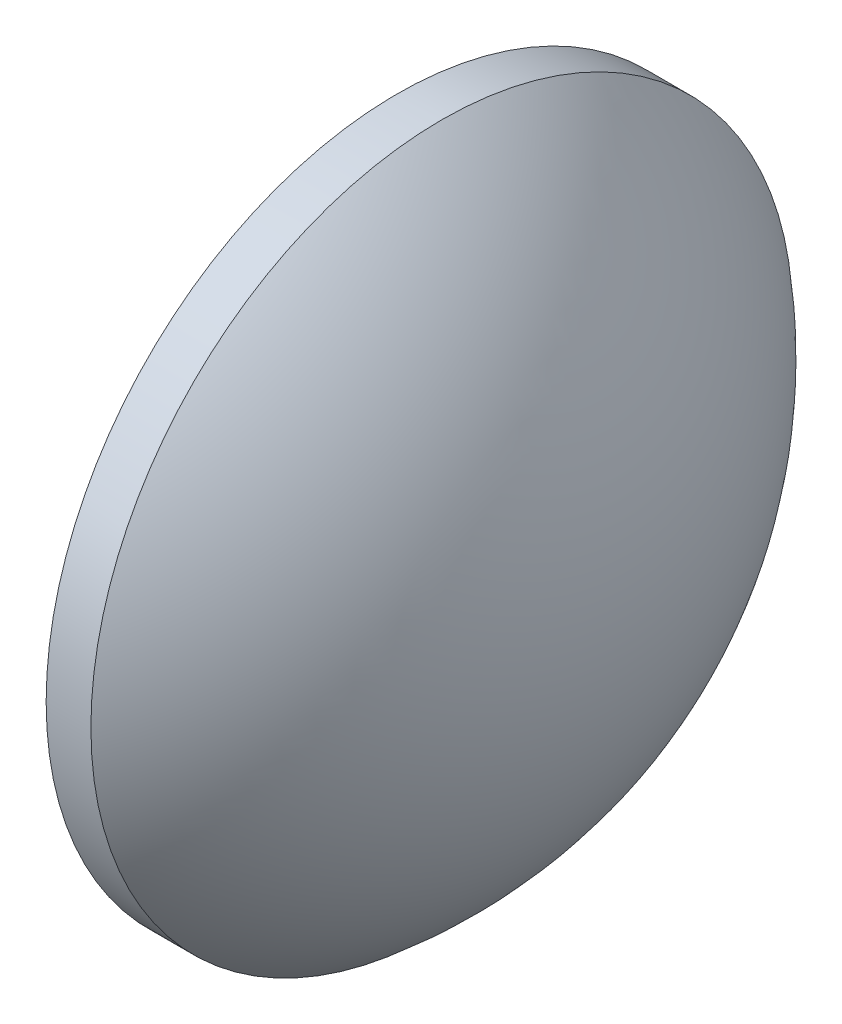
SolidWorks part; units mm, degrees
ref_plane "前视基准面" through (0, 0, 0) normal (0, 0, 1) x (1, 0, 0)
ref_plane "上视基准面" through (0, 0, 0) normal (0, 1, 0) x (1, 0, 0)
ref_plane "右视基准面" through (0, 0, 0) normal (1, 0, 0) x (0, 0, -1)
sketch "草图1" plane through (0, 0, 0) normal (0, 0, 1) x (1, 0, 0)
  line L0 (332.1519, 126.8001) -> (385.9348, 126.8001) construction
  line L1 (350.7782, 126.8001) -> (350.7782, 134.8001)
  line L2 (350.7782, 134.8001) -> (351.7982, 134.8001)
  line L3 (355.5782, 126.8001) -> (350.7782, 126.8001)
  arc A0 (355.5782, 126.8001) -> (351.7982, 134.8001) centre (345.2226, 126.8001) ccw
revolve "旋转1" add sketch "草图1" angle 360 about L0
